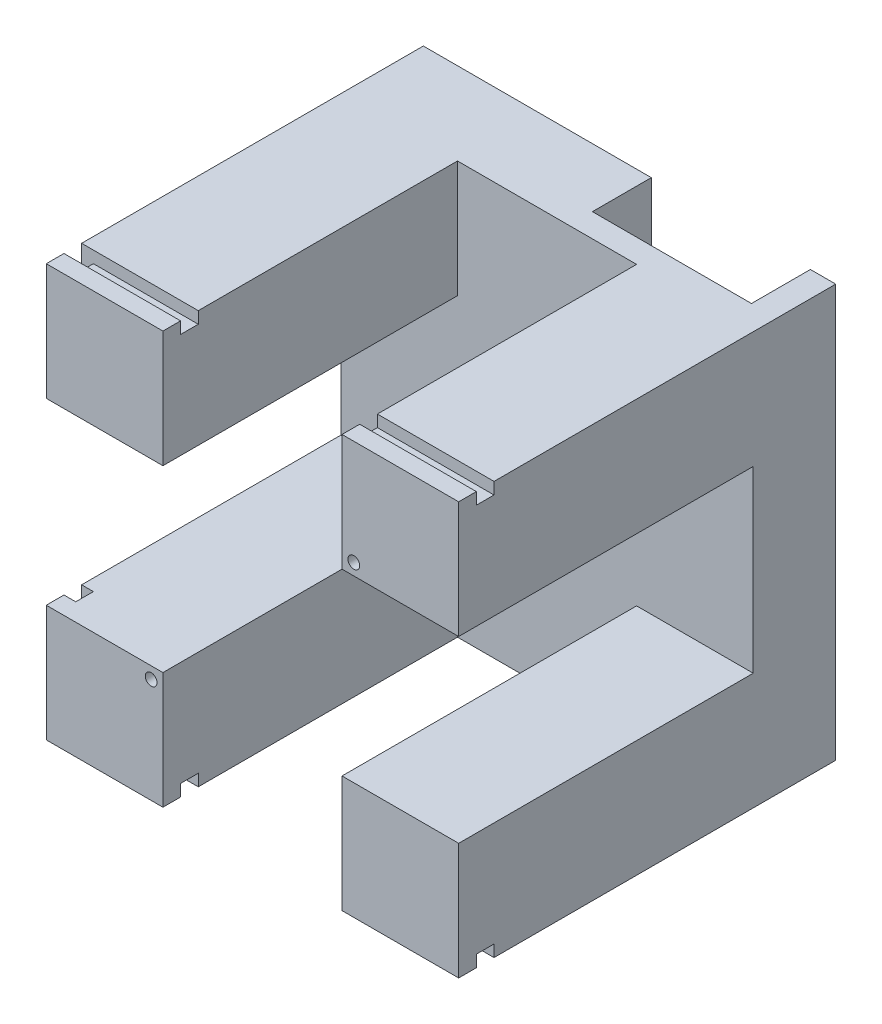
SolidWorks part; units mm, degrees
ref_plane "Plan de face" through (0, 0, 0) normal (0, 0, 1) x (1, 0, 0)
ref_plane "Plan de dessus" through (0, 0, 0) normal (0, 1, 0) x (1, 0, 0)
ref_plane "Plan de droite" through (0, 0, 0) normal (1, 0, 0) x (0, 0, -1)
sketch "Esquisse1" plane through (0, 0, 0) normal (0, 0, 1) x (1, 0, 0)
  line L1 (0, 0) -> (-70, 0)
  line L2 (0, 0) -> (0, 70)
  line L3 (0, 70) -> (-70, 70)
  line L4 (-70, 0) -> (-70, 70)
  dimension "D1" = 70
  dimension "D2" = 70
extrude "Boss.-Extru.1" add sketch "Esquisse1" along normal blind 64
sketch "Esquisse2" plane through (0, 0, 64) normal (0, 0, 1) x (1, 0, 0)
  line L0 (-70, 70) -> (-70, 0) construction
  line L1 (-70, 50.2) -> (0, 50.2)
  line L2 (-70, 50.2) -> (-70, 19.8)
  line L3 (-70, 19.8) -> (0, 19.8)
  line L4 (0, 50.2) -> (0, 19.8)
  line L5 (0, 0) -> (0, 70) construction
  line L6 (-70, 0) -> (0, 0) construction
  line L7 (-19.8, 0) -> (-50.2, 0)
  line L8 (-19.8, 0) -> (-19.8, 70)
  line L9 (-19.8, 70) -> (-50.2, 70)
  line L10 (-50.2, 0) -> (-50.2, 70)
  line L11 (0, 70) -> (-70, 70) construction
  line M5 (0, 0) -> (0, 70)
  line M6 (0, 70) -> (-70, 70)
  line M7 (-70, 70) -> (-70, 0)
  line M8 (-70, 0) -> (0, 0)
  dimension "D1" = 30.4
  dimension "D2" = 19.8
  dimension "D3" = 30.4
  dimension "D4" = 19.8
extrude "Enlèv. mat.-Extru.1" cut sketch "Esquisse2" against normal blind 50 contours L10 L1 L8 M6 | L10 L3 L8 L1 | L8 L3 L1 M5 | L3 L10 L1 M7 | L10 L8 L3 M8
sketch "Esquisse5" plane through (-70, 0, 0) normal (-1, 0, 0) x (0, 0, 1)
  line L0 (64, 70) -> (0, 70) construction
  line L1 (61, 70) -> (58, 70)
  line L2 (61, 70) -> (61, 68)
  line L3 (61, 68) -> (58, 68)
  line L4 (58, 70) -> (58, 68)
  line L5 (64, 0) -> (0, 0) construction
  line L6 (61, 0) -> (58, 0)
  line L7 (61, 0) -> (61, 2)
  line L8 (61, 2) -> (58, 2)
  line L9 (58, 0) -> (58, 2)
  line L10 (64, 19.8) -> (64, 0) construction
  line L11 (64, 70) -> (64, 50.2) construction
  dimension "D1" = 3
  dimension "D2" = 3
  dimension "D3" = 2
  dimension "D4" = 2
  dimension "D5" = 3
  dimension "D6" = 3
extrude "Enlèv. mat.-Extru.3" cut sketch "Esquisse5" against normal through all
sketch "Esquisse6" plane through (0, 70, 0) normal (0, 1, 0) x (1, 0, 0)
  line L0 (-50.2, -61) -> (-70, -61) construction
  line L1 (-70, -58) -> (-68, -58)
  line L2 (-70, -58) -> (-70, -61)
  line L3 (-70, -61) -> (-68, -61)
  line L4 (-68, -58) -> (-68, -61)
  dimension "D1" = 2
extrude "Enlèv. mat.-Extru.4" cut sketch "Esquisse6" against normal through all
sketch "Esquisse7" plane through (0, 0, 64) normal (0, 0, 1) x (1, 0, 0)
  line L0 (-50.2, 0) -> (-50.2, 19.8) construction
  line L1 (-70, 19.8) -> (-50.2, 19.8) construction
  circle A0 centre (-52.2, 17.8) radius 1
  dimension "D1" = 2
  dimension "D2" = 2
  dimension "D3" = 2
extrude "Enlèv. mat.-Extru.5" cut sketch "Esquisse7" against normal through all
sketch "Esquisse8" plane through (0, 0, 0) normal (0, 0, -1) x (-1, 0, 0)
  line L0 (60.2, 17.8) -> (60.2, 0)
  line L1 (70, 0) -> (0, 0) construction
  line L2 (60.2, 0) -> (44.2, 0)
  line L3 (44.2, 0) -> (44.2, 17.8)
  line L4 (44.2, 17.8) -> (60.2, 17.8)
  circle A0 centre (52.2, 17.8) radius 8
  circle M2 centre (52.2, 17.8) radius 1
  line M4 (0, 0) -> (70, 0)
  dimension "D1" = 16
extrude "Enlèv. mat.-Extru.7" cut sketch "Esquisse8" against normal blind 10 contours A0 L3 L0 M4 | L4 A0 M2 | L4 A0 M2
sketch "Esquisse9" plane through (0, 0, 0) normal (0, 0, -1) x (-1, 0, 0)
  line L0 (46.2, 17.8) -> (46.2, 0)
  line L1 (46.2, 0) -> (44.2, 0)
  line L2 (44.2, 0) -> (44.2, 28.7424)
  line L3 (44.2, 28.7424) -> (60.1757, 28.7424)
  line L4 (60.1757, 28.7424) -> (60.2, 17.8)
  line L5 (60.2, 17.8) -> (60.2, 0)
  line L6 (60.2, 17.8) -> (60.2, 0) construction
  line L7 (58.2, 17.8) -> (58.2, 0)
  line L8 (58.2, 0) -> (60.2, 0)
  circle A0 centre (52.2, 17.8) radius 6
  line M1 (60.2, 17.8) -> (60.2, 0)
  line M7 (44.2, 0) -> (44.2, 17.8)
  arc M8 (44.2, 17.8) -> (60.2, 17.8) centre (52.2, 17.8) cw
  dimension "D1" = 12
extrude "Boss.-Extru.2" add sketch "Esquisse9" against normal blind 3.8 contours A0 L7 L8 L1 L0 M1 M8 M7
sketch "Esquisse10" plane through (0, 0, 0) normal (0, 0, -1) x (-1, 0, 0)
  line L0 (70, 0) -> (58.2, 0) construction
  line L1 (38.7, 18.1) -> (65.7, 18.1)
  line L2 (38.7, 18.1) -> (38.7, 0)
  line L3 (38.7, 0) -> (65.7, 0)
  line L4 (65.7, 18.1) -> (65.7, 0)
  arc A0 (58.1926, 18.098) -> (46.2076, 18.1013) centre (52.2, 17.8) ccw
  arc A2 (58.2, 17.8) -> (46.2, 17.8) centre (52.2, 17.8) ccw construction
  line M3 (58.2, 17.8) -> (58.2, 0)
  line M4 (58.2, 0) -> (70, 0)
  line M8 (0, 0) -> (46.2, 0)
  line M9 (46.2, 0) -> (46.2, 17.8)
  dimension "D1" = 27
  dimension "D2" = 5.5
extrude "Enlèv. mat.-Extru.8" cut sketch "Esquisse10" against normal blind 10 contours L1 L2 M8 M9 | L4 L1 M3 M4
sketch "Esquisse11" plane through (0, 18.1, 0) normal (0, -1, 0) x (1, 0, 0)
  line L0 (-38.7, 10) -> (-38.7, 0) construction
  line L1 (-65.7, 10) -> (-65.7, 0) construction
  line L2 (-60.1944, 10) -> (-65.7, 10) construction
  line L3 (-38.7, 10) -> (-44.2056, 10) construction
  circle A0 centre (-41.7, 7) radius 1.25
  circle A1 centre (-62.7, 7) radius 1.25
  dimension "D1" = 2.5
  dimension "D2" = 2.5
  dimension "D3" = 3
  dimension "D4" = 3
  dimension "D5" = 3
  dimension "D6" = 3
extrude "Enlèv. mat.-Extru.9" cut sketch "Esquisse11" against normal blind 15
sketch3d "Esquisse3D2"
  line L0 (-35, 35, 57.383) -> (-35, 35, -1.6203) construction
  point P2 (0, 35, 0)
  point P5 (0, 35, 64)
  dimension "D1" = 35
  dimension "D2" = 35
  dimension "D3" = 35
pattern_circular "Répétition circulaire1" count 2 every 180 about axis through (-35, 35, 0) along (0, 0, 1) of "Enlèv. mat.-Extru.5", "Enlèv. mat.-Extru.7", "Enlèv. mat.-Extru.8"
